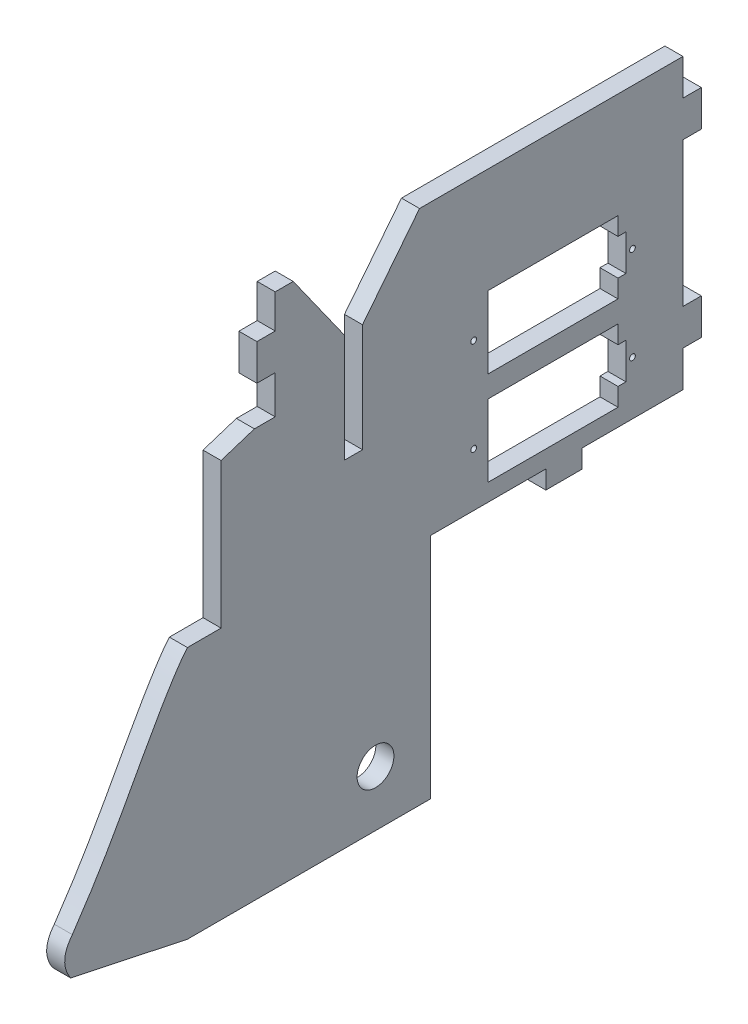
SolidWorks part; units mm, degrees
ref_plane "Front Plane" through (0, 0, 0) normal (0, 0, 1) x (1, 0, 0)
ref_plane "Top Plane" through (0, 0, 0) normal (0, 1, 0) x (1, 0, 0)
ref_plane "Right Plane" through (0, 0, 0) normal (1, 0, 0) x (0, 0, -1)
sketch "Sketch1" plane through (0, 0, 0) normal (1, 0, 0) x (0, 0, -1)
  line L1 (-35.8775, -25.4) -> (35.8775, -25.4)
  line L2 (-35.8775, -25.4) -> (-35.8775, 25.4)
  line L3 (-35.8775, 25.4) -> (35.8775, 25.4)
  line L4 (35.8775, -25.4) -> (35.8775, 25.4)
  line L5 (-35.8775, -25.4) -> (35.8775, 25.4) construction
  line L6 (-35.8775, 25.4) -> (35.8775, -25.4) construction
  point P0 (0, 0)
  dimension "D1" = 50.8
  dimension "D2" = 71.755
extrude "main body" add sketch "Sketch1" along normal blind 3.175
sketch "Sketch2" plane through (3.175, 0, 0) normal (1, 0, 0) x (0, 0, -1)
  line L0 (-35.8775, 19.431) -> (-39.1033, 19.431)
  line L1 (-35.8775, 25.4) -> (-35.8775, -25.4) construction
  line L2 (-39.1033, 19.431) -> (-39.1033, 13.081)
  line L3 (-39.1033, 13.081) -> (-35.8775, 13.081)
  line L4 (-35.8775, 13.081) -> (-35.8775, 19.431)
  line L5 (35.8775, 19.05) -> (39.1033, 19.05)
  line L6 (35.8775, -25.4) -> (35.8775, 25.4) construction
  line L7 (39.1033, 19.05) -> (39.1033, 12.7)
  line L8 (39.1033, 12.7) -> (35.8775, 12.7)
  line L9 (35.8775, 25.4) -> (-35.8775, 25.4) construction
  line L10 (35.8775, 12.7) -> (35.8775, 19.05)
  line L11 (35.8775, 25.4) -> (-35.8775, 25.4) construction
  line L12 (35.8775, -19.05) -> (35.8775, -12.7)
  line L13 (35.8775, -12.7) -> (39.1033, -12.7)
  line L14 (39.1033, -12.7) -> (39.1033, -19.05)
  line L15 (39.1033, -19.05) -> (35.8775, -19.05)
  line L16 (-35.8775, -25.4) -> (35.8775, -25.4) construction
  line L17 (18.0975, -25.4) -> (11.7475, -25.4)
  line L18 (11.7475, -25.4) -> (11.7475, -28.6258)
  line L19 (11.7475, -28.6258) -> (18.0975, -28.6258)
  line L20 (18.0975, -28.6258) -> (18.0975, -25.4)
  line L21 (-35.8775, 25.4) -> (-35.8775, -25.4) construction
  dimension "D1" = 3.2258
  dimension "D2" = 6.35
  dimension "D3" = 3.2258
  dimension "D4" = 6.35
  dimension "D5" = 6.35
  dimension "D6" = 5.969
  dimension "D7" = 3.2258
  dimension "D8" = 6.35
  dimension "D9" = 6.35
  dimension "D10" = 47.625
  dimension "D11" = 6.35
  dimension "D13" = 3.2258
extrude "tabs" add sketch "Sketch2" against normal blind 3.175
ref_plane "Plane1" through (0, 0, 0) normal (0, 0, 1) x (1, 0, 0)
sketch "Sketch3" plane through (0, 0, 0) normal (-1, 0, 0) x (0, 0, 1)
  line L0 (51.3269, -54.7103) -> (71.5739, -54.7103) construction
  line L1 (51.3269, -61.1707) -> (71.8725, -61.1707) construction
  line L2 (51.3269, -21.0812) -> (51.3269, -65.5378) construction
  line L3 (51.3269, -58.0438) -> (72.9169, -58.0438) construction
  line L4 (51.3269, -21.0812) -> (45.4025, -21.0812)
  line L5 (35.8775, -25.4) -> (35.8775, -57.3232)
  line L6 (45.4025, -21.0812) -> (45.4025, 4.4592)
  line L7 (35.8775, -25.4) -> (35.8775, 6.35)
  line L8 (51.3269, -65.5378) -> (42.8625, -65.5378)
  line L9 (35.8775, 6.35) -> (39.5346, 6.35)
  line L10 (42.8625, -65.5378) -> (35.8775, -57.3232)
  line L11 (35.8775, 13.081) -> (35.8775, -25.4) construction
  line L12 (71.8725, -61.1707) -> (51.3269, -65.5378)
  line L24 (39.5346, 6.35) -> (45.4025, 4.4592)
  spline S0 degree 3 poles (71.5739, -54.7103) (65.7071, -46.0919) (62.4105, -39.3502) (53.3534, -23.3895) (51.3269, -21.0812) knots 0 0 0 0 0.673726 1 1 1 1
  spline S1 degree 2 poles (71.5739, -54.7103) (74.1022, -57.8684) (71.8725, -61.1707) knots 0 0 0 1 1 1
  dimension "D2" = 31.75
  dimension "D3" = 9.525
  dimension "D7" = 20.5455
  dimension "D8" = 15.4494
  dimension "D9" = 20.247
  dimension "D10" = 21.59
  dimension "D11" = 44.4566
  dimension "D12" = 31.9232
  dimension "D15" = 4.3671
  dimension "D16" = 7.494
  dimension "D17" = 10.8275
extrude "nose section" add sketch "Sketch3" against normal blind 3.175
sketch "Sketch8" plane through (0, 0, 0) normal (-1, 0, 0) x (0, 0, 1)
  line L0 (35.8775, -25.4) -> (-11.7475, -25.4) construction
  line L2 (35.8775, 25.4) -> (35.8775, 19.431) construction
  line B0 (-1.5875, -5.842) -> (-1.5875, 6.858)
  line B1 (-1.5875, -5.842) -> (-24.4475, -5.842)
  line B2 (-24.4475, -5.842) -> (-24.4475, -2.667)
  line B3 (-1.5875, 6.858) -> (-24.4475, 6.858)
  line B4 (-24.4475, -2.667) -> (-25.8445, -2.667)
  line B5 (-25.8445, -2.667) -> (-25.8445, 3.683)
  line B6 (-24.4475, 3.683) -> (-25.8445, 3.683)
  line B7 (-24.4475, 3.683) -> (-24.4475, 6.858)
  circle B8 centre (-26.9875, 0.508) radius 0.508
  circle B9 centre (0.9525, 0.508) radius 0.508
  line B10 (-1.5875, -22.352) -> (-1.5875, -9.652)
  line B11 (-1.5875, -22.352) -> (-24.4475, -22.352)
  line B12 (-24.4475, -22.352) -> (-24.4475, -19.177)
  line B13 (-1.5875, -9.652) -> (-24.4475, -9.652)
  line B14 (-24.4475, -19.177) -> (-25.8445, -19.177)
  line B15 (-25.8445, -19.177) -> (-25.8445, -12.827)
  line B16 (-24.4475, -12.827) -> (-25.8445, -12.827)
  line B17 (-24.4475, -12.827) -> (-24.4475, -9.652)
  circle B18 centre (-26.9875, -16.002) radius 0.508
  circle B19 centre (0.9525, -16.002) radius 0.508
  dimension "D1" = 9.398
  dimension "D2" = 25.908
  dimension "D3" = 54.229
  dimension "D4" = 54.229
sketch_block_instance "Block1-3"
sketch_block "Block1" parameters "D5"=1.016, "D6"=1.016, "D9"=2.1092, "D1"=27.94, "D2"=6.35, "D3"=22.86, "D4"=12.7, "D7"=1.397, "D8"=6.35
sketch_block_instance "Block1-4"
extrude "cut for motors" cut sketch "Sketch8" against normal through all
sketch "Sketch9" plane through (0, 0, 0) normal (-1, 0, 0) x (0, 0, 1)
  line L1 (-35.8775, 25.4) -> (35.8775, 25.4) construction
  line L2 (20.5105, -6.3459) -> (23.6855, -6.3459)
  line L3 (20.5105, -6.3459) -> (20.5105, 12.7041)
  line L4 (20.0025, 25.4) -> (23.1775, 25.4)
  line L5 (23.6855, -6.3459) -> (23.6855, 12.7)
  line L6 (20.5105, -6.3459) -> (23.1775, 25.4) construction
  line L8 (20.0025, 25.4) -> (23.6855, -6.3459) construction
  line L10 (23.6855, 12.7) -> (32.7025, 25.4)
  line L11 (23.1775, 25.4) -> (32.7025, 25.4)
  line L12 (20.5105, 12.7041) -> (10.4775, 25.4)
  line L13 (10.4775, 25.4) -> (20.0025, 25.4)
  line L14 (35.8775, 25.4) -> (35.8775, 19.431) construction
  point P0 (21.844, 9.527)
  dimension "D1" = 12.192
  dimension "D2" = 3.175
  dimension "D3" = 31.75
  dimension "D4" = 9.525
  dimension "D5" = 3.175
  dimension "D6" = 9.525
  dimension "D7" = 3.175
extrude "slot for firewall" cut sketch "Sketch9" against normal through all
sketch "Sketch10" plane through (0, 0, 0) normal (-1, 0, 0) x (0, 0, 1)
  line L0 (35.8775, -57.3232) -> (35.8775, -25.4)
  line L2 (35.8775, -57.3232) -> (42.8625, -65.5378)
  line L3 (42.8625, -65.5378) -> (8.5725, -65.5378)
  line L4 (35.8775, -25.4) -> (8.5725, -25.4)
  line L6 (35.8775, -25.4) -> (-11.7475, -25.4) construction
  line L7 (8.5725, -25.4) -> (8.5725, -65.5378)
  dimension "D2" = 34.29
extrude "extension for axle" add sketch "Sketch10" against normal blind 3.175
sketch "Sketch11" plane through (0, 0, 0) normal (-1, 0, 0) x (0, 0, 1)
  line L0 (8.5725, -65.5378) -> (51.3269, -65.5378) construction
  line L1 (8.5725, -25.4) -> (8.5725, -65.5378) construction
  circle A0 centre (18.2245, -55.753) radius 3.2385
  dimension "D1" = 6.477
  dimension "D2" = 9.7848
  dimension "D3" = 9.652
extrude "cut for axle" cut sketch "Sketch11" against normal through all
